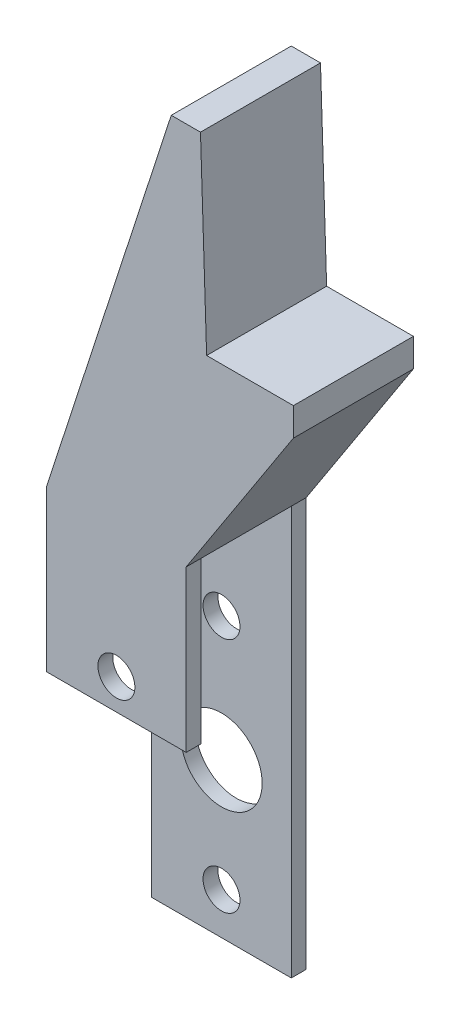
SolidWorks part; units mm, degrees
ref_plane "Front Plane" through (0, 0, 0) normal (0, 0, 1) x (1, 0, 0)
ref_plane "Top Plane" through (0, 0, 0) normal (0, 1, 0) x (1, 0, 0)
ref_plane "Right Plane" through (0, 0, 0) normal (1, 0, 0) x (0, 0, -1)
sketch "Sketch1" plane through (0, 0, 0) normal (0, 0, 1) x (1, 0, 0)
  line L0 (-110.5146, 1.2624) -> (-96.2144, 1.2624)
  line L1 (-96.2144, 1.2624) -> (-96.2144, 43.1216)
  line L2 (-96.2144, 43.1216) -> (-85.2304, 60.0356)
  line L3 (-94.1201, 62.924) -> (-85.2304, 62.924)
  line L4 (-94.1201, 62.924) -> (-94.75, 82.4248)
  line L5 (-94.75, 82.4248) -> (-97.7443, 82.4248)
  line L6 (-110.5146, 1.2624) -> (-110.5146, 43.1216)
  line L7 (-110.5146, 43.1216) -> (-97.7443, 82.4248)
  line L8 (-85.2304, 62.924) -> (-85.2304, 60.0356)
extrude "Boss-Extrude3" add sketch "Sketch1" along normal blind 12.2936
sketch "Sketch2" plane through (-96.2144, 0, 0) normal (1, 0, 0) x (0, 0, -1)
  line L0 (-12.2936, 1.2624) -> (-10.7696, 1.2624)
  line L1 (-12.2936, 1.2624) -> (0, 1.2624) construction
  line L2 (-10.7696, 1.2624) -> (-1.524, 1.2624)
  line L3 (0, 1.2624) -> (-1.524, 1.2624)
  line L4 (-1.524, 1.2624) -> (-1.524, 43.1216)
  line L5 (-1.524, 43.1216) -> (-10.7696, 43.1216)
  line L6 (-10.7696, 43.1216) -> (-10.7696, 26.6624)
  line L8 (-10.7696, 26.6624) -> (-12.2936, 26.6624)
  line L9 (-12.2936, 1.2624) -> (-12.2936, 43.1216) construction
  line L10 (-12.2936, 26.6624) -> (-12.2936, 1.2624)
  line M2 (0, 43.1216) -> (-12.2936, 43.1216)
  line M3 (-12.2936, 43.1216) -> (-12.2936, 1.2624)
  line M4 (-12.2936, 1.2624) -> (0, 1.2624)
extrude "Cut-Extrude3" cut sketch "Sketch2" against normal blind 14.3002 contours L6 L8 L4 M3 M4 M2
sketch "Sketch3" plane through (0, 0, 0) normal (0, 0, -1) x (-1, 0, 0)
  line L0 (103.3645, 1.2624) -> (103.3645, 5.5296) construction
  line L1 (110.5146, 1.2624) -> (96.2144, 1.2624) construction
  line L2 (103.3645, 5.5296) -> (103.3645, 17.0358) construction
  line L3 (103.3645, 17.0358) -> (103.3645, 29.812) construction
  line L4 (103.3645, 29.812) -> (103.3645, 65.1274) construction
  line L5 (97.7443, 82.4248) -> (110.5146, 43.1216) construction
  circle A0 centre (103.3645, 5.5296) radius 1.8923
  circle A1 centre (103.3645, 29.812) radius 1.8923
  circle A2 centre (103.3645, 17.0358) radius 4.1681
extrude "Cut-Extrude4" cut sketch "Sketch3" against normal blind 14.3002
